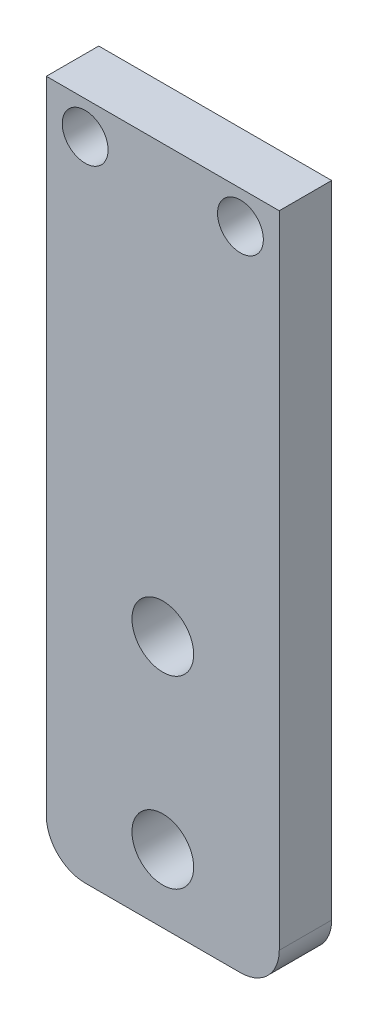
SolidWorks part; units mm, degrees
ref_plane "Front Plane" through (0, 0, 0) normal (0, 0, 1) x (1, 0, 0)
ref_plane "Top Plane" through (0, 0, 0) normal (0, 1, 0) x (1, 0, 0)
ref_plane "Right Plane" through (0, 0, 0) normal (1, 0, 0) x (0, 0, -1)
ref_plane "Mounting Plane" through (0, -20.955, 0) normal (0, 1, 0) x (1, 0, 0)
sketch "Sketch1" plane through (0, 0, 0) normal (0, 0, 1) x (1, 0, 0)
  line L0 (0, 16.51) -> (0, 4.445) construction
  line L1 (-7.62, 44.45) -> (7.62, 44.45)
  line L2 (-7.62, 44.45) -> (-7.62, 0)
  line L3 (-7.62, 0) -> (7.62, 0)
  line L4 (7.62, 44.45) -> (7.62, 0)
  line L5 (5.08, 42.291) -> (-5.08, 42.291) construction
  line L6 (0, 42.291) -> (0, 16.51) construction
  circle A0 centre (0, 4.445) radius 2.0193
  circle A1 centre (0, 16.51) radius 2.0193
  circle A2 centre (-5.08, 42.291) radius 1.5
  circle A3 centre (5.08, 42.291) radius 1.5
  dimension "D3" = 4.0386
  dimension "D8" = 3
  dimension "D1" = 15.24
  dimension "D2" = 44.45
  dimension "D4" = 4.445
  dimension "D5" = 12.065
  dimension "D6" = 10.16
  dimension "D7" = 2.159
extrude "Boss-Extrude1" add sketch "Sketch1" along normal blind 3.429
fillet "Fillet1" radius 2.54 2 edges at (7.62, 0, 1.7145) (-7.62, 0, 1.7145)
